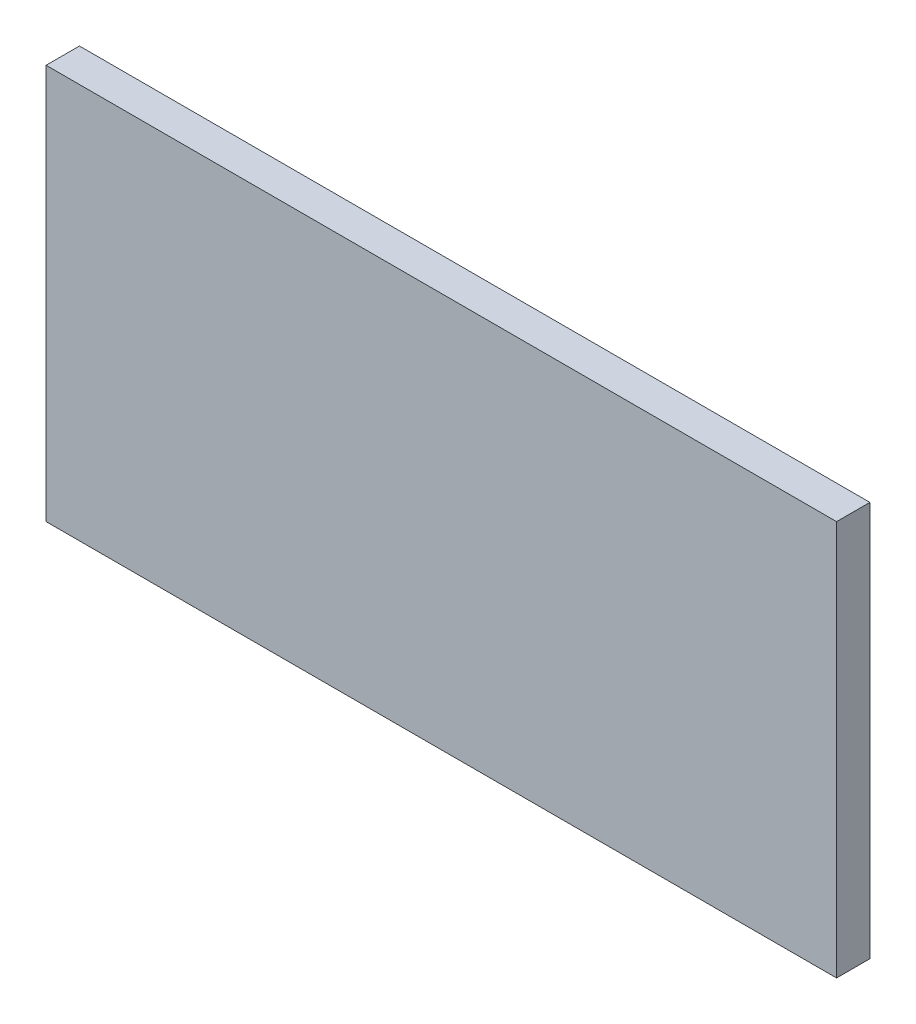
SolidWorks part; units mm, degrees
ref_plane "Plane1" through (0, 0, 0) normal (0, 0, 1) x (1, 0, 0)
ref_plane "Plane2" through (0, 0, 0) normal (0, 1, 0) x (1, 0, 0)
ref_plane "Plane3" through (0, 0, 0) normal (1, 0, 0) x (0, 0, -1)
sketch "Sketch1" plane through (0, 0, 0) normal (0, 0, 1) x (1, 0, 0)
  line L1 (17.78, -8.89) -> (-17.78, -8.89)
  line L2 (17.78, -8.89) -> (17.78, 8.89)
  line L3 (17.78, 8.89) -> (-17.78, 8.89)
  line L4 (-17.78, -8.89) -> (-17.78, 8.89)
  line L5 (17.78, -8.89) -> (-17.78, 8.89) construction
  line L6 (17.78, 8.89) -> (-17.78, -8.89) construction
  point P0 (0, 0)
  dimension "D1" = 17.78
  dimension "D2" = 35.56
extrude "Boss-Extrude1" add sketch "Sketch1" along normal blind 1.5
